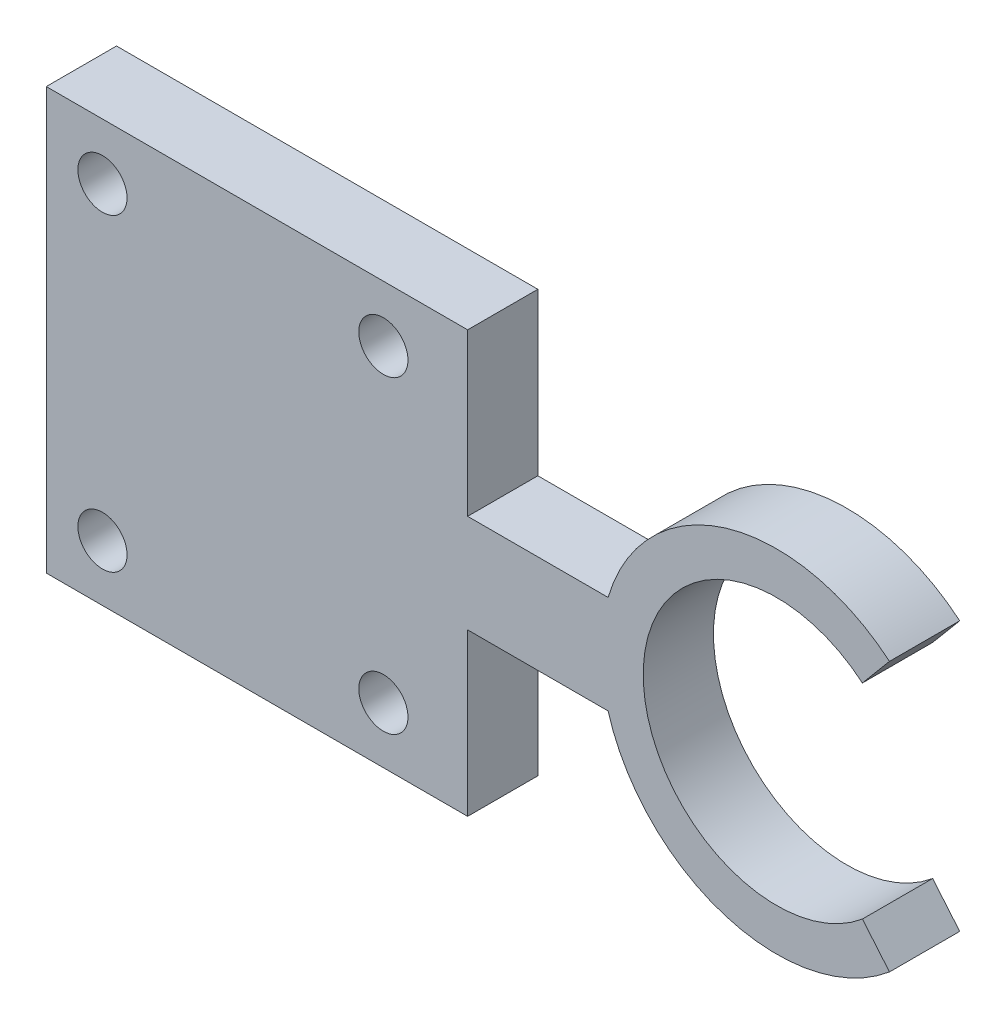
SolidWorks part; units mm, degrees
ref_plane "Plano frontal" through (0, 0, 0) normal (0, 0, 1) x (1, 0, 0)
ref_plane "Plano superior" through (0, 0, 0) normal (0, 1, 0) x (1, 0, 0)
ref_plane "Plano direito" through (0, 0, 0) normal (1, 0, 0) x (0, 0, -1)
sketch "Esboço1" plane through (0, 0, 0) normal (0, 0, 1) x (1, 0, 0)
  line L0 (7.0707, 8.4265) -> (0, 0) construction
  line L1 (0, 0) -> (7.0707, -8.4265) construction
  line L2 (-11, 0) -> (-19.8171, 0) construction
  arc A0 (7.0707, 8.4265) -> (7.0707, -8.4265) centre (0, 0) ccw
  point P6 (0, 0)
  dimension "D1" = 11
  dimension "D2" = 100
sketch "Esboço14" plane through (0, 0, 0) normal (0, 1, 0) x (1, 0, 0)
  line L0 (-12, 2.5) -> (-52, 2.5)
  line L1 (-52, -2.5) -> (-52, 2.5)
  line L6 (-12, -2.5) -> (-52, -2.5)
  line L7 (-12, 2.5) -> (-12, -2.5)
  point P3 (-12, 0)
  dimension "D2" = 5
  dimension "D4" = 40
  dimension "D7" = 12
extrude "Ressalto-extrusão1" add sketch "Esboço14" along normal mid plane 7
sketch3d "3DSketch2"
  line L0 (0, 0, 0) -> (7.0707, -8.4265, 0) construction
  line L1 (8.0348, -9.5756, 2.5) -> (6.1065, -7.2774, 2.5)
  line L2 (6.1065, -7.2774, 2.5) -> (6.1065, -7.2774, -2.5)
  line L3 (6.1065, -7.2774, -2.5) -> (8.0348, -9.5756, -2.5)
  line L4 (8.0348, -9.5756, -2.5) -> (8.0348, -9.5756, 2.5)
  line L5 (-12, -3.5, 2.5) -> (-12, -3.5, -2.5) construction
  point P4 (6.1065, -7.2774, 0)
  point P10 (7.0707, -8.4265, 0)
  dimension "D3" = 3
  dimension "D4" = 1.5
sweep "Varredura1" add profiles "3DSketch2" path "Esboço1"
sketch "Esboço15" plane through (0, 0, 2.5) normal (0, 0, 1) x (1, 0, 0)
  line L0 (-52, 3.5) -> (-52, -3.5) construction
  line L1 (-22, 15) -> (-52, 15)
  line L2 (-22, 15) -> (-22, -15)
  line L3 (-22, -15) -> (-52, -15)
  line L4 (-52, 15) -> (-52, -15)
  line L5 (-22, 15) -> (-52, -15) construction
  line L6 (-22, -15) -> (-52, 15) construction
  circle A0 centre (-48, 11) radius 1.75
  circle A1 centre (-28, 11) radius 1.75
  circle A2 centre (-28, -11) radius 1.75
  circle A3 centre (-48, -11) radius 1.75
  point P0 (-37, 0)
  dimension "D3" = 3.5
  dimension "D1" = 30
  dimension "D2" = 30
  dimension "D4" = 4
  dimension "D5" = 4
  dimension "D6" = 2
  dimension "D7" = 2
extrude "Ressalto-extrusão2" add sketch "Esboço15" against normal up to surface (5 mm away) up to face at (-14.8267, 0, -2.5)
